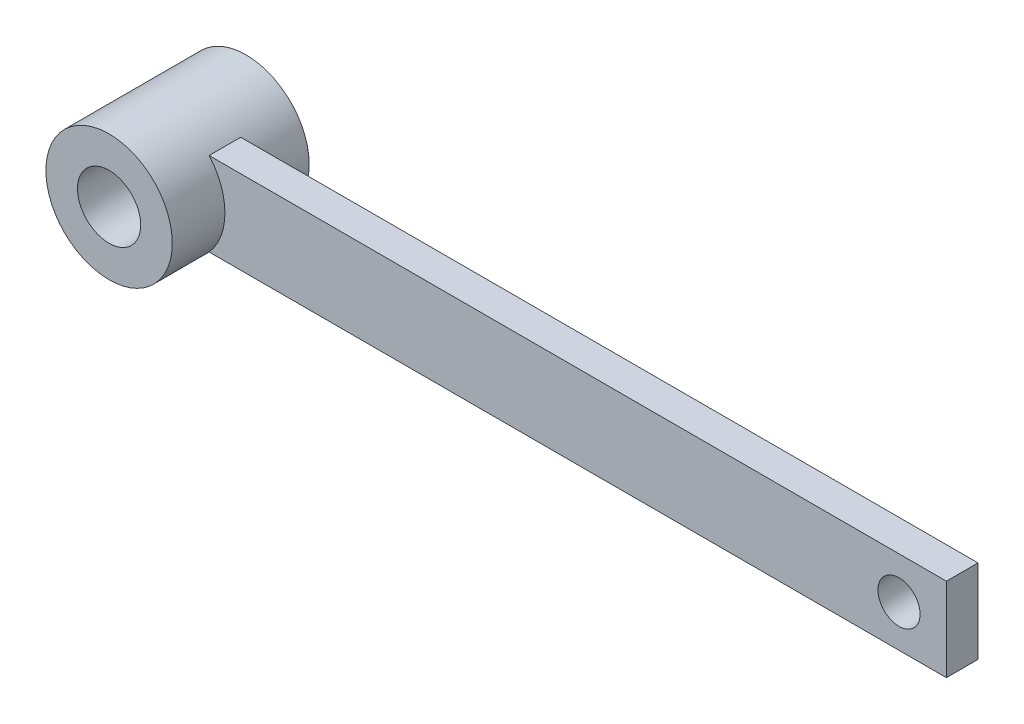
SolidWorks part; units mm, degrees
ref_plane "Front Plane" through (0, 0, 0) normal (0, 0, 1) x (1, 0, 0)
ref_plane "Top Plane" through (0, 0, 0) normal (0, 1, 0) x (1, 0, 0)
ref_plane "Right Plane" through (0, 0, 0) normal (1, 0, 0) x (0, 0, -1)
sketch "Sketch1" plane through (0, 0, 0) normal (0, 0, 1) x (1, 0, 0)
  line L0 (3, 0) -> (28.6244, 0) construction
  line L1 (4.5, -3.9686) -> (4.5, 3.9686)
  line L2 (4.5, 3.9686) -> (74.5, 3.9686)
  line L3 (74.5, 3.9686) -> (74.5, -3.9686)
  line L4 (4.5, -3.9686) -> (74.5, -3.9686)
  circle A0 centre (0, 0) radius 6
  circle A1 centre (0, 0) radius 3
  circle A2 centre (70, 0) radius 2
  point P9 (4.5, 0)
  point P12 (74.5, 0)
  dimension "D1" = 12
  dimension "D2" = 6
  dimension "D5" = 4
  dimension "D6" = 70
  dimension "D3" = 4.5
  dimension "D4" = 70
extrude "Boss-Extrude1" add sketch "Sketch1" along normal blind 3
sketch "Sketch2" plane through (0, 0, 3) normal (0, 0, 1) x (1, 0, 0)
  circle A0 centre (0, 0) radius 6
  circle A1 centre (0, 0) radius 3
  dimension "D1" = 12
  dimension "D2" = 6
extrude "Boss-Extrude2" add sketch "Sketch2" along normal blind 5 and the other way blind 8
